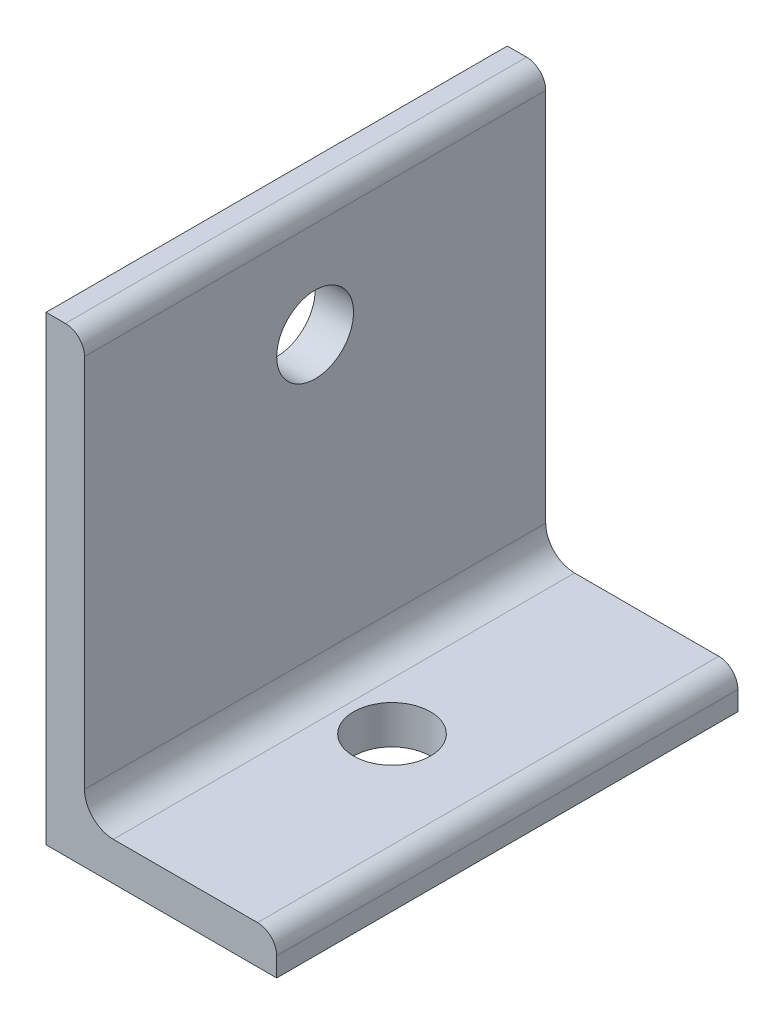
SolidWorks part; units mm, degrees
ref_plane "Plane1" through (0, 0, 0) normal (0, 0, 1) x (1, 0, 0)
ref_plane "Plane2" through (0, 0, 0) normal (0, 1, 0) x (1, 0, 0)
ref_plane "Plane3" through (0, 0, 0) normal (1, 0, 0) x (0, 0, -1)
sketch "Sketch1" plane through (0, 0, 0) normal (0, 0, 1) x (1, 0, 0)
  line L0 (0, 0) -> (0, 76.2)
  line L1 (0, 76.2) -> (3.1801, 76.2)
  line L2 (6.35, 73.0301) -> (6.35, 11.1125)
  line L3 (11.1125, 6.35) -> (34.9301, 6.35)
  line L4 (38.1, 3.1801) -> (38.1, 0)
  line L5 (38.1, 0) -> (0, 0)
  arc A0 (38.1, 3.1801) -> (34.9301, 6.35) centre (34.9301, 3.1801) ccw
  arc A1 (3.1801, 76.2) -> (6.35, 73.0301) centre (3.1801, 73.0301) cw
  arc A2 (11.1125, 6.35) -> (6.35, 11.1125) centre (11.1125, 11.1125) cw
  circle A3 centre (0, 0) radius 3.175 construction
  dimension "D2" = 3.1801
  dimension "Radius_1" = 4.7625
  dimension "Radius_2" = 3.175
  dimension "D1" = 6.35
  dimension "V_leg" = 76.2
  dimension "H_leg" = 38.1
  dimension "Thickness" = 6.35
  dimension "Flat_wid" = 3.1801
extrude "BaseSteelAngle" add sketch "Sketch1" along normal mid plane 76.2
sketch "Sketch2" plane through (0, 0, 0) normal (0, -1, 0) x (1, 0, 0)
  line L1 (38.1, 38.1) -> (38.1, -38.1) construction
  line L2 (0, 0) -> (38.1, 0) construction
  line L3 (0, 38.1) -> (0, -38.1) construction
  circle A0 centre (19.05, 0) radius 6.35
  dimension "D1" = 12.7
  dimension "D2" = 19.05
extrude "Cut-Extrude1" cut sketch "Sketch2" against normal up to next
sketch "Sketch3" plane through (0, 0, 0) normal (-1, 0, 0) x (0, 0, 1)
  line L0 (38.1, 76.2) -> (38.1, 0) construction
  line L1 (38.1, 76.2) -> (-38.1, 76.2) construction
  line L2 (0, 0) -> (0, 76.2) construction
  line L3 (38.1, 0) -> (-38.1, 0) construction
  circle A0 centre (0, 57.15) radius 6.35
  dimension "D1" = 12.7
  dimension "D2" = 38.1
  dimension "D3" = 19.05
extrude "Cut-Extrude2" cut sketch "Sketch3" against normal through all
equation "\"Flat_wid@Sketch1\" = ((sgn(\"Thickness@Sketch1\" - \"Radius_2@Sketch1\") +1)*(\"Thickness@Sketch1\" - \"Radius_2@Sketch1\"))/2 +0.0002"
equation "\"D1@Sketch1\" = \"Thickness@Sketch1\""
equation "\"D2@Sketch1\" = \"Flat_wid@Sketch1\""
